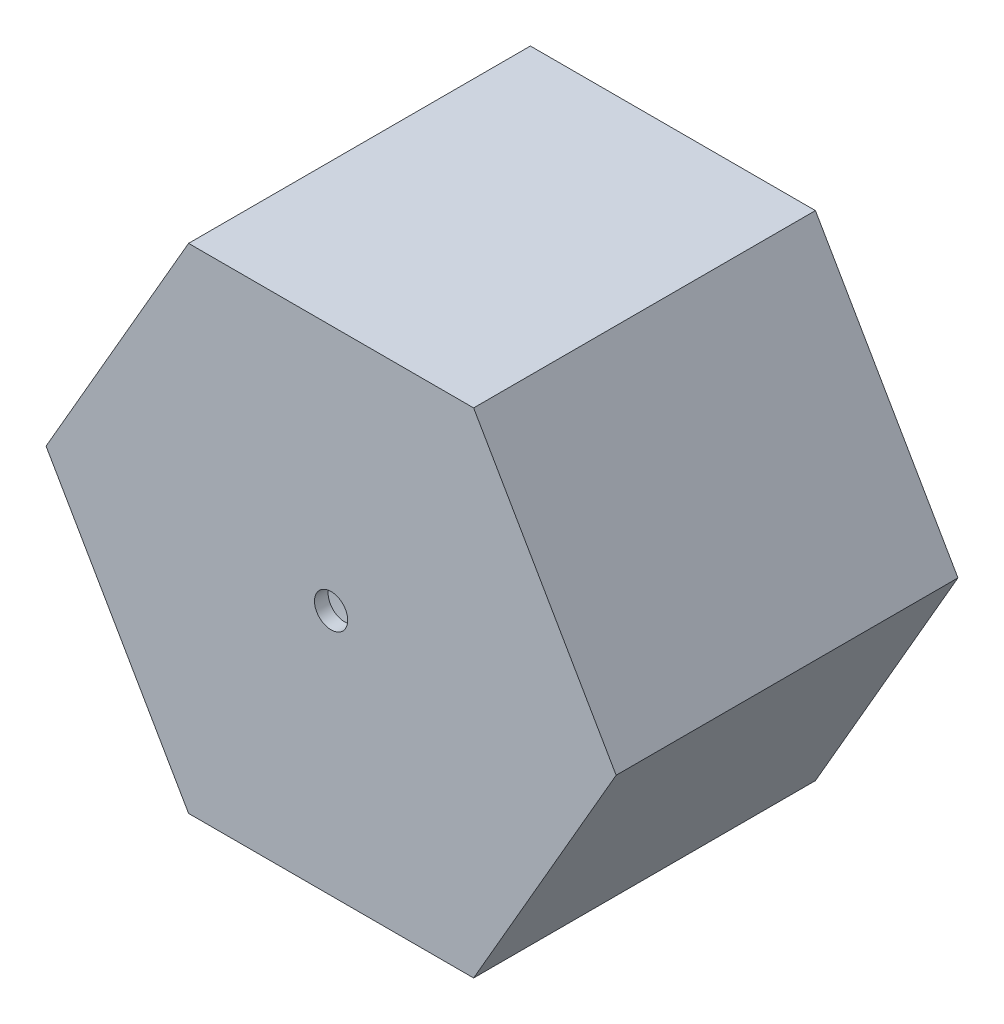
SolidWorks part; units mm, degrees
ref_plane "Ebene vorne" through (0, 0, 0) normal (0, 0, 1) x (1, 0, 0)
ref_plane "Ebene oben" through (0, 0, 0) normal (0, 1, 0) x (1, 0, 0)
ref_plane "Ebene rechts" through (0, 0, 0) normal (1, 0, 0) x (0, 0, -1)
sketch "Skizze1" plane through (0, 0, 0) normal (0, 0, 1) x (1, 0, 0)
  line L1 (15.0111, 0) -> (7.5056, 13)
  line L2 (7.5056, 13) -> (-7.5056, 13)
  line L3 (-7.5056, 13) -> (-15.0111, 0)
  line L4 (-15.0111, 0) -> (-7.5056, -13)
  line L5 (-7.5056, -13) -> (7.5056, -13)
  line L6 (7.5056, -13) -> (15.0111, 0)
  circle A0 centre (0, 0) radius 13 construction
extrude "Aufsatz-Linear austragen1" add sketch "Skizze1" along normal blind 18
hole_wizard "Ø16.0 (16) Durchmesser Bohrung1" positions "Skizze3" profile "Skizze4" hole size "Ø16.0" standard "ANSI Metrisch"
sketch "Skizze3" plane through (0, 0, 0) normal (0, 0, -1) x (-1, 0, 0)
  point P0 (0, 0)
sketch "Skizze4" plane through (0, 0, 0) normal (1, 0, 0) x (0, 1, 0)
  line L0 (0, 0) -> (0, 17.8069)
  line L1 (0, 17.8069) -> (8, 13)
  line L2 (8, 13) -> (8, 0)
  line L5 (8, 0) -> (0, 0)
  line L10 (0, 17.8069) -> (-8, 13) construction
  line L11 (0, -6.35) -> (0, 107.95) construction
  dimension "Bohrerdurchmesser" = 16
  dimension "Bohrungstiefe" = 13
  dimension "Spitzenwinkel" = 118
hole_wizard "Ø1.75 (1.75) Durchmesser Bohrung1" positions "Skizze6" profile "Skizze7" hole size "Ø1.75" standard "ANSI Metrisch" end condition through all
sketch "Skizze6" plane through (0, 0, 18) normal (0, 0, 1) x (1, 0, 0)
  point P0 (0, 0)
sketch "Skizze7" plane through (0, 0, 18) normal (1, 0, 0) x (0, -1, 0)
  line L0 (0, 0) -> (0, 18)
  line L1 (0, 18) -> (0.875, 18)
  line L2 (0.875, 18) -> (0.875, 0)
  line L5 (0.875, 0) -> (0, 0)
  line L11 (0, -6.35) -> (0, 107.95) construction
  dimension "Bohrerdurchmesser" = 1.75
  dimension "Bohrungstiefe" = 18
